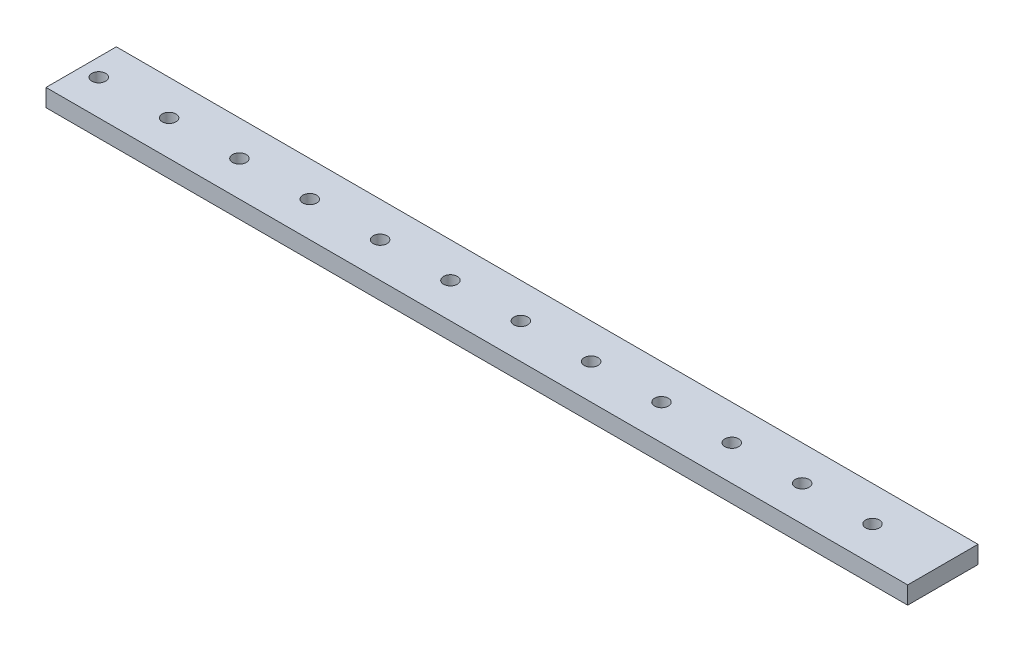
SolidWorks part; units mm, degrees
material "Lexan"
ref_plane "Front Plane" through (0, 0, 0) normal (0, 0, 1) x (1, 0, 0)
ref_plane "Top Plane" through (0, 0, 0) normal (0, 1, 0) x (1, 0, 0)
ref_plane "Right Plane" through (0, 0, 0) normal (1, 0, 0) x (0, 0, -1)
sketch "Sketch1" plane through (0, 0, 0) normal (0, 1, 0) x (1, 0, 0)
  line L1 (0, 0) -> (406.4, 0)
  line L2 (0, 0) -> (0, 25.4)
  line L3 (0, 25.4) -> (406.4, 25.4)
  line L4 (406.4, 0) -> (406.4, 25.4)
  dimension "D1" = 25.4
  dimension "D2" = 406.4
extrude "Boss-Extrude1" add sketch "Sketch1" along normal blind 6.35
sketch "Sketch2" plane through (0, 6.35, 0) normal (0, 1, 0) x (1, 0, 0)
  line L0 (406.4, 12.7) -> (0, 12.7) construction
  line L1 (406.4, 0) -> (406.4, 25.4) construction
  line L2 (0, 25.4) -> (0, 0) construction
  circle A0 centre (381, 12.7) radius 2.4892
  circle A1 centre (355.6, 12.7) radius 2.4892
  circle A2 centre (330.2, 12.7) radius 2.4892
  circle A3 centre (304.8, 12.7) radius 2.4892
  circle A4 centre (279.4, 12.7) radius 2.4892
  circle A5 centre (254, 12.7) radius 2.4892
  circle A6 centre (228.6, 12.7) radius 2.4892
  circle A7 centre (203.2, 12.7) radius 2.4892
  circle A8 centre (177.8, 12.7) radius 2.4892
  circle A9 centre (152.4, 12.7) radius 2.4892
  circle A10 centre (127, 12.7) radius 2.4892
  circle A11 centre (101.6, 12.7) radius 2.4892
  dimension "D1" = 25.4
  dimension "D2" = 4.9784
  dimension "D3" = 12
extrude "Cut-Extrude1" cut sketch "Sketch2" against normal through all both
sketch "Sketch3" plane through (0, 0, 0) normal (0, -1, 0) x (1, 0, 0)
  circle A2 centre (63.5, -12.7) radius 2.3781
  circle A3 centre (38.1, -12.7) radius 2.2074
extrude "Cut-Extrude2" cut sketch "Sketch3" against normal through all
sketch "Sketch4" plane through (0, 0, 0) normal (-1, 0, 0) x (0, 0, 1)
  line L1 (-25.4, 6.35) -> (0, 6.35)
  line L2 (-25.4, 6.35) -> (-25.4, 0)
  line L3 (-25.4, 0) -> (0, 0)
  line L4 (0, 6.35) -> (0, 0)
extrude "Cut-Extrude3" cut sketch "Sketch4" against normal blind 95.25
